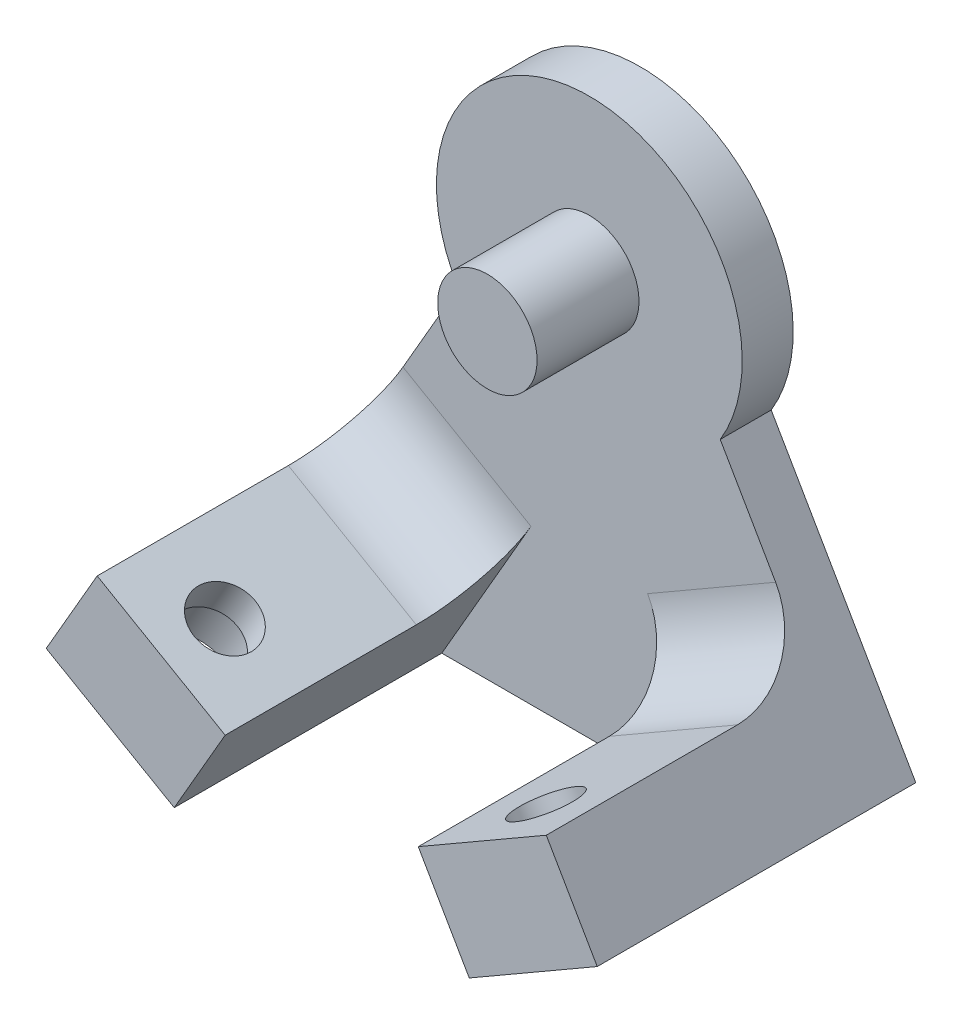
SolidWorks part; units mm, degrees
ref_plane "정면" through (0, 0, 0) normal (0, 0, 1) x (1, 0, 0)
ref_plane "윗면" through (0, 0, 0) normal (0, 1, 0) x (1, 0, 0)
ref_plane "우측면" through (0, 0, 0) normal (1, 0, 0) x (0, 0, -1)
sketch "스케치1" plane through (0, 0, 0) normal (0, 0, 1) x (1, 0, 0)
  line L0 (0, 0) -> (0, -17.7997) construction
  line L1 (0, 0) -> (-6.3, -10.9119) construction
  line L2 (-3.7885, -12.3619) -> (-8.8115, -9.4619) construction
  line L3 (-8.8115, -9.4619) -> (-10.8115, -12.926)
  line L4 (-10.8115, -12.926) -> (-5.7885, -15.826)
  line L5 (-5.7885, -15.826) -> (-3.7885, -12.3619) construction
  line L6 (-8.8115, -9.4619) -> (-5.1378, -3.0989)
  line L7 (-5.7885, -15.826) -> (5.7885, -15.826)
  line L8 (10.8115, -12.926) -> (5.7885, -15.826)
  line L9 (8.8115, -9.4619) -> (10.8115, -12.926)
  line L10 (8.8115, -9.4619) -> (5.1378, -3.0989)
  arc A0 (5.1378, -3.0989) -> (-5.1378, -3.0989) centre (0, 0) ccw
  point P8 (-6.3, -10.9119)
  point P13 (0, -15.826)
  dimension "D1" = 12
  dimension "D2" = 12.6
  dimension "D3" = 30
  dimension "D4" = 5.8
  dimension "D5" = 4
extrude "보스-돌출1" add sketch "스케치1" along normal blind 2
sketch "스케치2" plane through (0, 0, 2) normal (0, 0, 1) x (1, 0, 0)
  line L0 (-5.7885, -15.826) -> (-10.8115, -12.926)
  line L1 (-5.7885, -15.826) -> (-3.7885, -12.3619)
  line L2 (-10.8115, -12.926) -> (-8.8115, -9.4619)
  line L3 (-3.7885, -12.3619) -> (-8.8115, -9.4619)
  line L4 (0, 0) -> (0, -15.826) construction
  line L5 (-5.7885, -15.826) -> (5.7885, -15.826) construction
  line L6 (5.7885, -15.826) -> (3.7885, -12.3619)
  line L7 (5.7885, -15.826) -> (10.8115, -12.926)
  line L8 (10.8115, -12.926) -> (8.8115, -9.4619)
  line L9 (3.7885, -12.3619) -> (8.8115, -9.4619)
  dimension "D1" = 12.6
extrude "보스-돌출2" add sketch "스케치2" along normal blind 10.5
sketch "스케치3" plane through (0, 0, 2) normal (0, 0, 1) x (1, 0, 0)
  circle A0 centre (0, 0) radius 1.95
  dimension "D1" = 3.9
extrude "보스-돌출3" add sketch "스케치3" along normal blind 4
fillet "필렛1" radius 3 2 edges at (-6.3, -10.9119, 2) (6.3, -10.9119, 2)
sketch "스케치4" plane through (-8.3, -14.376, 0) normal (-0.5, -0.866, 0) x (0.866, -0.5, 0)
  line L0 (-2.9, 12.5) -> (2.9, 12.5) construction
  circle A0 centre (0, 10) radius 1.2
  dimension "D1" = 2.4
  dimension "D2" = 2.5
extrude "컷-돌출1" cut sketch "스케치4" against normal through all
sketch "스케치5" plane through (-8.3, -14.376, 0) normal (-0.5, -0.866, 0) x (0.866, -0.5, 0)
  circle A0 centre (0, 10) radius 2
  dimension "D1" = 4
extrude "컷-돌출2" cut sketch "스케치5" against normal blind 2.6
mirror "대칭 복사1" about plane through (0, 0, 0) normal (1, 0, 0) of "컷-돌출1", "컷-돌출2"
